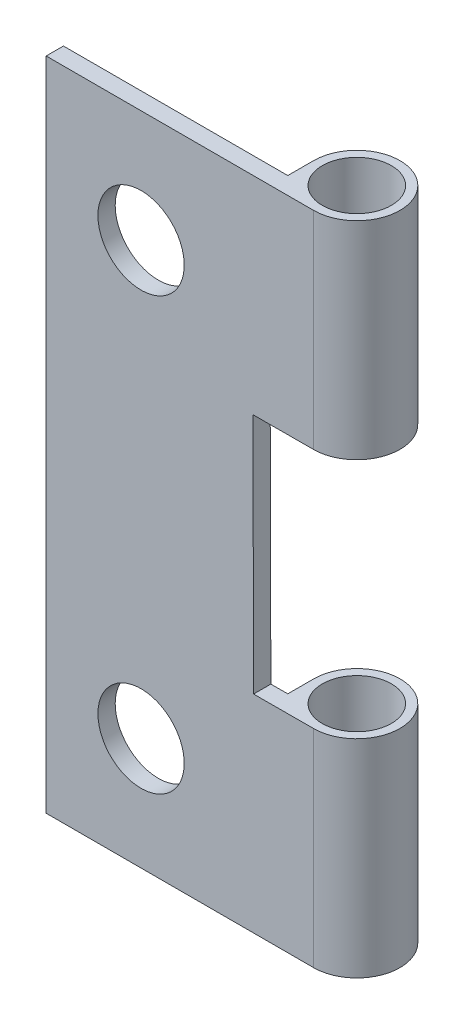
SolidWorks part; units mm, degrees
ref_plane "前视" through (0, 0, 0) normal (0, 0, 1) x (1, 0, 0)
ref_plane "上视" through (0, 0, 0) normal (0, 1, 0) x (1, 0, 0)
ref_plane "右视" through (0, 0, 0) normal (1, 0, 0) x (0, 0, -1)
sketch "草图1" plane through (0, 0, 0) normal (0, 0, 1) x (1, 0, 0)
  line L0 (-6.5, -19) -> (6.5, -19)
  line L1 (-6.5, -19) -> (-6.5, 19)
  line L2 (6.5, -19) -> (6.5, 19)
  line L3 (-6.5, 19) -> (6.5, 19)
  line L4 (-6.5, -19) -> (6.5, 19) construction
  line L5 (6.5, -19) -> (-6.5, 19) construction
  point P1 (0, 0)
extrude "凸台-拉伸1" add sketch "草图1" along normal blind 1
sketch "草图2" plane through (0, 19, 0) normal (0, 1, 0) x (1, 0, 0)
  line L0 (6.5, -1) -> (9, -1)
  line L1 (6.5, -1) -> (6.5, 1.5)
  arc A0 (9, -1) -> (6.5, 1.5) centre (9, 1.5) ccw
  circle A1 centre (9, 1.5) radius 2
extrude "凸台-拉伸2" add sketch "草图2" against normal blind 38
sketch "草图3" plane through (0, 0, 1) normal (0, 0, 1) x (1, 0, 0)
  line L0 (5.5191, -7.0095) -> (12.519, -6.9904)
  line L1 (5.5191, -7.0095) -> (5.481, 6.9904)
  line L2 (12.519, -6.9904) -> (12.4809, 7.0095)
  line L3 (5.481, 6.9904) -> (12.4809, 7.0095)
  line L4 (5.5191, -7.0095) -> (12.4809, 7.0095) construction
  line L5 (12.519, -6.9904) -> (5.481, 6.9904) construction
  line L7 (9, -19) -> (9, 19) construction
  point P1 (9, 0)
extrude "切除-拉伸1" cut sketch "草图3" against normal blind 10
sketch "草图4" plane through (0, 0, 0) normal (0, 0, -1) x (-1, 0, 0)
  line L0 (-6.5, 19) -> (6.5, 19) construction
  line L2 (6.5, 19) -> (6.5, -19) construction
  circle A0 centre (1, 12.5) radius 2.5
  circle A1 centre (1, -12.5) radius 2.5
  dimension "D1" = 6.5
  dimension "D2" = 5.5
extrude "切除-拉伸2" cut sketch "草图4" against normal blind 2
